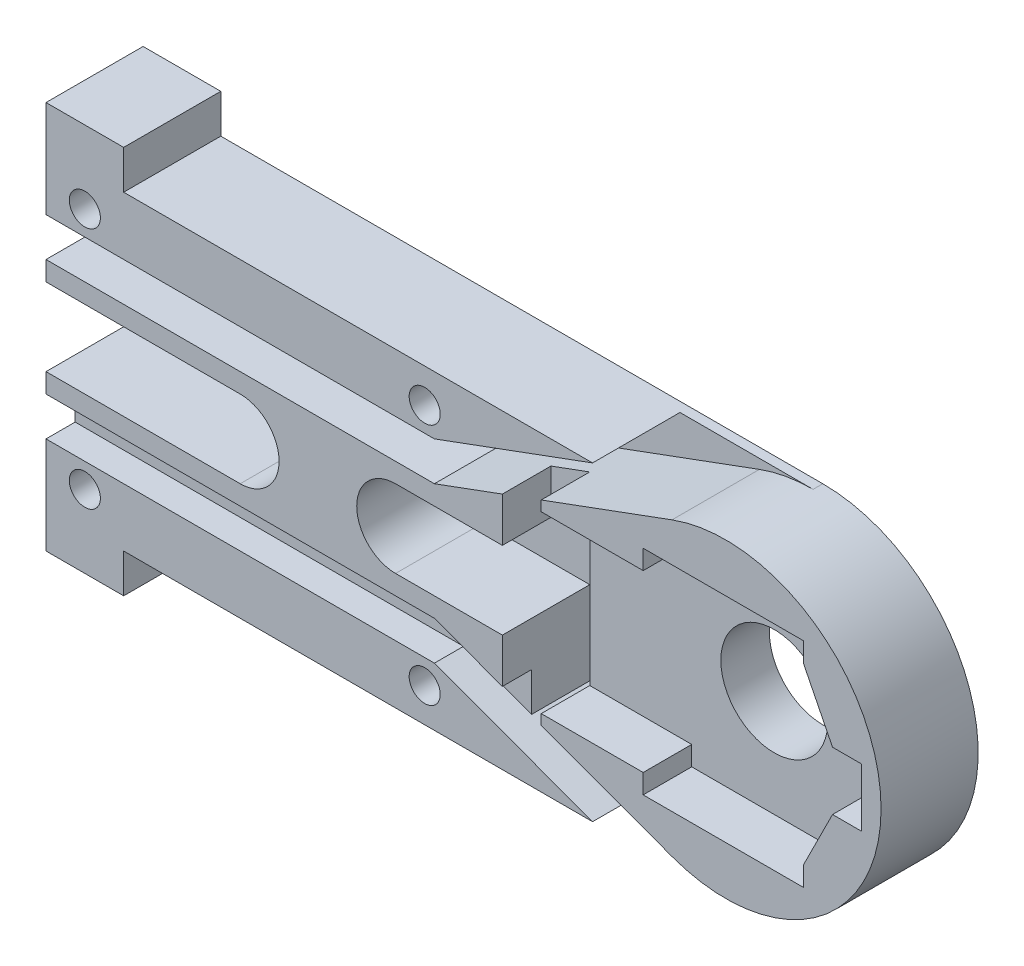
SolidWorks part; units mm, degrees
ref_plane "Front Plane" through (0, 0, 0) normal (0, 0, 1) x (1, 0, 0)
ref_plane "Top Plane" through (0, 0, 0) normal (0, 1, 0) x (1, 0, 0)
ref_plane "Right Plane" through (0, 0, 0) normal (1, 0, 0) x (0, 0, -1)
sketch "Sketch1" plane through (0, 0, 0) normal (0, 0, 1) x (1, 0, 0)
  line L0 (37.2876, 8) -> (37.2876, 0)
  line L1 (37.2876, 8) -> (72.2876, 8)
  line L2 (72.2876, -8) -> (37.2876, -8)
  line L3 (37.2876, -8) -> (37.2876, 0)
  line L4 (37.2876, 8) -> (37.2876, 10)
  line L5 (72.2876, 0) -> (37.2876, 0) construction
  line L6 (37.2876, 10) -> (41.2876, 10)
  line L7 (41.2876, 10) -> (41.2876, 8)
  line L9 (37.2876, -8) -> (37.2876, -10)
  line L10 (37.2876, -10) -> (41.2876, -10)
  line L11 (41.2876, -10) -> (41.2876, -8)
  circle A0 centre (72.2876, 0) radius 8
extrude "Boss-Extrude1" add sketch "Sketch1" along normal blind 5
sketch "Sketch4" plane through (0, 0, 0) normal (0, 0, 1) x (1, 0, 0)
  circle A0 centre (72.2876, 0) radius 2.75
extrude "Pot Hole" cut sketch "Sketch4" along normal through all
sketch "Sketch3" plane through (28.2876, 0, 0) normal (0, 0, 1) x (1, 0, 0)
  line L26 (44, 0) -> (51, 0) construction
  line L27 (44, 0) -> (34.5, 0) construction
  line L28 (44, 0) -> (44, -5.5) construction
  line L29 (44, 0) -> (44, 5.5) construction
  line L30 (51, 0) -> (51, 1.5)
  line L31 (51, 1.5) -> (49.5, 1.5)
  line L32 (49.5, 1.5) -> (48, 1.5) construction
  line L33 (48, 1.5) -> (48, 4.5) construction
  line L34 (49.5, 1.5) -> (48, 4.5)
  line L35 (48, 4.5) -> (48, 5.5)
  line L36 (48, 5.5) -> (44, 5.5)
  line L37 (44, 5.5) -> (39.75, 5.5)
  line L38 (39.75, 5.5) -> (39.75, 4.5)
  line L39 (39.75, 4.5) -> (34.5, 4.5)
  line L40 (34.5, 4.5) -> (34.5, 0)
  line L41 (51, 0) -> (51, -1.5)
  line L42 (51, -1.5) -> (49.5, -1.5)
  line L43 (49.5, -1.5) -> (48, -1.5) construction
  line L44 (48, -1.5) -> (48, -4.5) construction
  line L45 (49.5, -1.5) -> (48, -4.5)
  line L46 (48, -4.5) -> (48, -5.5)
  line L47 (48, -5.5) -> (44, -5.5)
  line L48 (44, -5.5) -> (39.75, -5.5)
  line L49 (39.75, -5.5) -> (39.75, -4.5)
  line L50 (39.75, -4.5) -> (34.5, -4.5)
  line L51 (34.5, -4.5) -> (34.5, 0)
extrude "Pot Insert" cut sketch "Sketch3" against normal blind 2.5 from offset 5
sketch "Sketch16" plane through (0, 0, 0) normal (0, 0, 1) x (1, 0, 0)
  line L0 (72.2876, -8) -> (65.4316, -8)
  line L2 (37.2876, -8) -> (37.2876, -5) construction
  line L4 (37.2876, -5) -> (57.2876, -5)
  line L5 (57.2876, -5) -> (65.4316, -8)
  line L7 (37.2876, -5) -> (37.2876, -3)
  line L9 (37.2876, -3) -> (57.2876, -3)
  line L10 (57.2876, -3) -> (69.5223, -7.5069)
  circle A1 centre (72.2876, 0) radius 8
extrude "Middle Flexion" cut sketch "Sketch16" along normal blind 2.5 from offset 3.5 contours A1 L10 L9 L7 L4 L5 L0
sketch "Sketch11" plane through (0, 0, 0) normal (0, 0, 1) x (1, 0, 0)
  line L0 (37.2876, 5) -> (37.2876, 3)
  line L1 (37.2876, 5) -> (57.2876, 5)
  line L2 (57.2876, 3) -> (69.5223, 7.5069)
  line L3 (57.2876, 3) -> (37.2876, 3)
  line L4 (57.2876, 5) -> (65.4316, 8)
  line L6 (65.4316, 8) -> (72.2876, 8)
  line L7 (37.2876, 8) -> (37.2876, 5) construction
  circle A0 centre (72.2876, 0) radius 8
extrude "Middle Extension" cut sketch "Sketch11" along normal blind 5.5 from offset 0.5
sketch "Sketch8" plane through (0, 0, 0) normal (0, 0, 1) x (1, 0, 0)
  line L0 (37.2876, 0) -> (37.2876, -2)
  line L1 (37.2876, -2) -> (47.2876, -2)
  line L2 (37.2876, 8) -> (37.2876, 0) construction
  line L9 (37.2876, 0) -> (47.2876, 0) construction
  line L10 (37.2876, 0) -> (37.2876, 2)
  line L11 (37.2876, 2) -> (47.2876, 2)
  arc A0 (47.2876, 2) -> (47.2876, -2) centre (47.2876, 0) cw
extrude "Proximal Flexion/Extension" cut sketch "Sketch8" along normal blind 5.5 from offset 0.5 contours A0 L11 L10 L0 L1
sketch "Sketch9" plane through (0, 0, 0) normal (0, 0, 1) x (1, 0, 0)
  line L0 (37.2876, 0) -> (39.2876, 0) construction
  line L1 (39.2876, 0) -> (39.2876, 6.25) construction
  line L2 (56.7876, 0) -> (56.7876, -6.25) construction
  line L3 (37.2876, 8) -> (37.2876, 0) construction
  line L4 (37.2876, 0) -> (47.2876, 0) construction
  line L5 (39.2876, 0) -> (56.7876, 0) construction
  line L6 (39.2876, 0) -> (39.2876, -6.25) construction
  line L7 (37.2876, 0) -> (37.2876, -8) construction
  line L8 (47.2876, 0) -> (55.2876, 0) construction
  line L9 (56.7876, 0) -> (56.7876, 6.25) construction
  circle A0 centre (47.2876, 0) radius 0.8
  circle A1 centre (56.7876, -6.25) radius 0.8
  circle A2 centre (39.2876, -6.25) radius 0.8
  circle A3 centre (55.2876, 0) radius 0.8
  circle A4 centre (39.2876, 6.25) radius 0.8
  circle A5 centre (56.7876, 6.25) radius 0.8
extrude "Screw Holes" cut sketch "Sketch9" along normal through all
sketch "Sketch12" plane through (0, 0, 0) normal (0, 0, 1) x (1, 0, 0)
  line L1 (60.7876, 2) -> (55.2876, 2)
  line L3 (60.7876, -2) -> (60.7876, -6.2893)
  line L4 (60.7876, -6.2893) -> (65.4316, -8)
  line L6 (60.7876, -2) -> (55.2876, -2)
  line L7 (57.2876, -5) -> (65.4316, -8) construction
  line L8 (60.7876, 2) -> (62.7876, 2)
  line L10 (65.4316, -8) -> (72.2876, -8)
  line L11 (62.7876, 2) -> (62.7876, -5.026)
  line L12 (57.2876, -3) -> (69.5223, -7.5069) construction
  line L13 (62.7876, -5.026) -> (69.5223, -7.5069)
  circle A0 centre (72.2876, 0) radius 8
  arc A1 (55.2876, 2) -> (55.2876, -2) centre (55.2876, 0) ccw
extrude "Cut-Extrude4" cut sketch "Sketch12" along normal blind 5.5 from offset 0.5 contours L1 A1 L6 L3 L4 L10 A0 L13 L11 L8
sketch "Sketch13" plane through (0, 0, 0) normal (0, 0, 1) x (1, 0, 0)
  line L0 (62.7876, 2) -> (60.7876, 2)
  line L2 (60.7876, 2) -> (60.7876, 4.2893)
  line L3 (57.2876, 3) -> (69.5223, 7.5069) construction
  line L4 (60.7876, 4.2893) -> (62.7876, 5.026)
  line L6 (62.7876, 5.026) -> (62.7876, 2)
extrude "Cut-Extrude5" cut sketch "Sketch13" against normal blind 2.5 from offset 5
